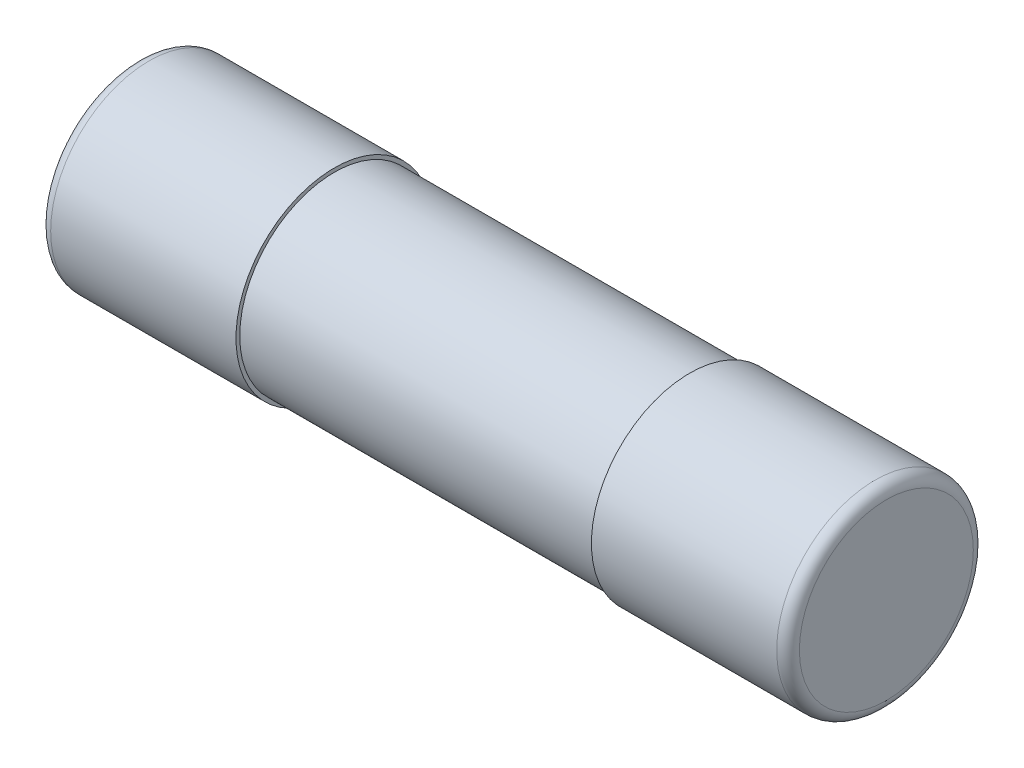
SolidWorks part; units mm, degrees
ref_plane "Plan de face" through (0, 0, 0) normal (0, 0, 1) x (1, 0, 0)
ref_plane "Plan de dessus" through (0, 0, 0) normal (0, 1, 0) x (1, 0, 0)
ref_plane "Plan de droite" through (0, 0, 0) normal (1, 0, 0) x (0, 0, -1)
sketch "Esquisse1" plane through (0, 0, 0) normal (1, 0, 0) x (0, 0, -1)
  circle A0 centre (0, 0) radius 2.5
extrude "Boss.-Extru.1" add sketch "Esquisse1" along normal mid plane 9.4
ref_plane "Plan1" through (0, 0, 0) normal (1, 0, 0) x (0, 0, -1)
sketch "Esquisse2" plane through (4.7, 0, 0) normal (1, 0, 0) x (0, 0, -1)
  circle A0 centre (0, 0) radius 2.6
extrude "Boss.-Extru.2" add sketch "Esquisse2" along normal blind 5.2
fillet "Congé1" radius 0.3 1 edges at (9.9, 0, -2.6)
mirror "Symétrie1" about plane through (0, 0, 0) normal (1, 0, 0) of "Congé1", "Boss.-Extru.2"
